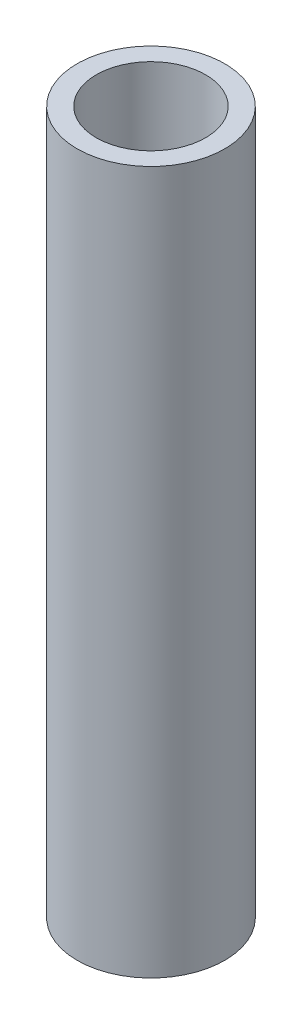
SolidWorks part; units mm, degrees
ref_plane "Front Plane" through (0, 0, 0) normal (0, 0, 1) x (1, 0, 0)
ref_plane "Top Plane" through (0, 0, 0) normal (0, 1, 0) x (1, 0, 0)
ref_plane "Right Plane" through (0, 0, 0) normal (1, 0, 0) x (0, 0, -1)
sketch "Sketch1" plane through (0, 0, 0) normal (0, 1, 0) x (1, 0, 0)
  circle A0 centre (0, 0) radius 7.8994
  circle A1 centre (0, 0) radius 10.668
  dimension "D1" = 21.336
  dimension "D2" = 15.7988
extrude "Boss-Extrude1" add sketch "Sketch1" along normal blind 101.6
